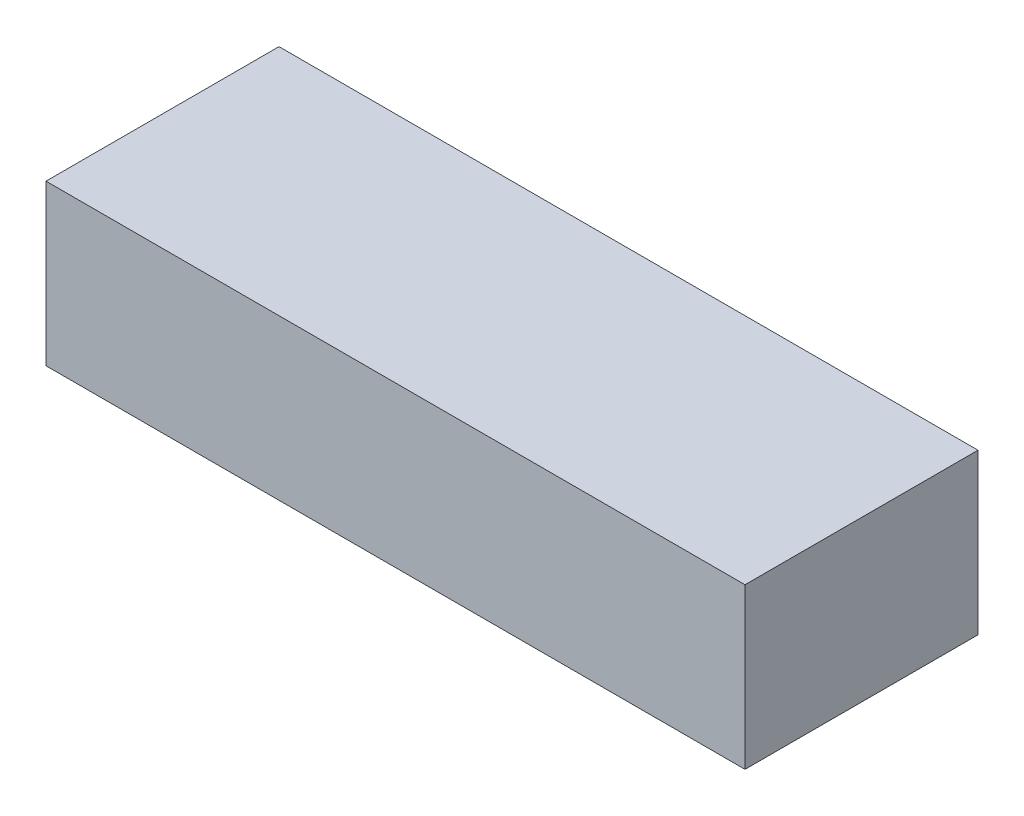
SolidWorks part; units mm, degrees
ref_plane "Front Plane" through (0, 0, 0) normal (0, 0, 1) x (1, 0, 0)
ref_plane "Top Plane" through (0, 0, 0) normal (0, 1, 0) x (1, 0, 0)
ref_plane "Right Plane" through (0, 0, 0) normal (1, 0, 0) x (0, 0, -1)
sketch "Sketch1" plane through (0, 0, 0) normal (0, 1, 0) x (1, 0, 0)
  line L1 (-153, 51) -> (153, 51)
  line L2 (-153, 51) -> (-153, -51)
  line L3 (-153, -51) -> (153, -51)
  line L4 (153, 51) -> (153, -51)
  line L5 (-153, 51) -> (153, -51) construction
  line L6 (-153, -51) -> (153, 51) construction
  point P0 (0, 0)
  dimension "D1" = 102
  dimension "D2" = 306
extrude "Boss-Extrude1" add sketch "Sketch1" along normal blind 70
